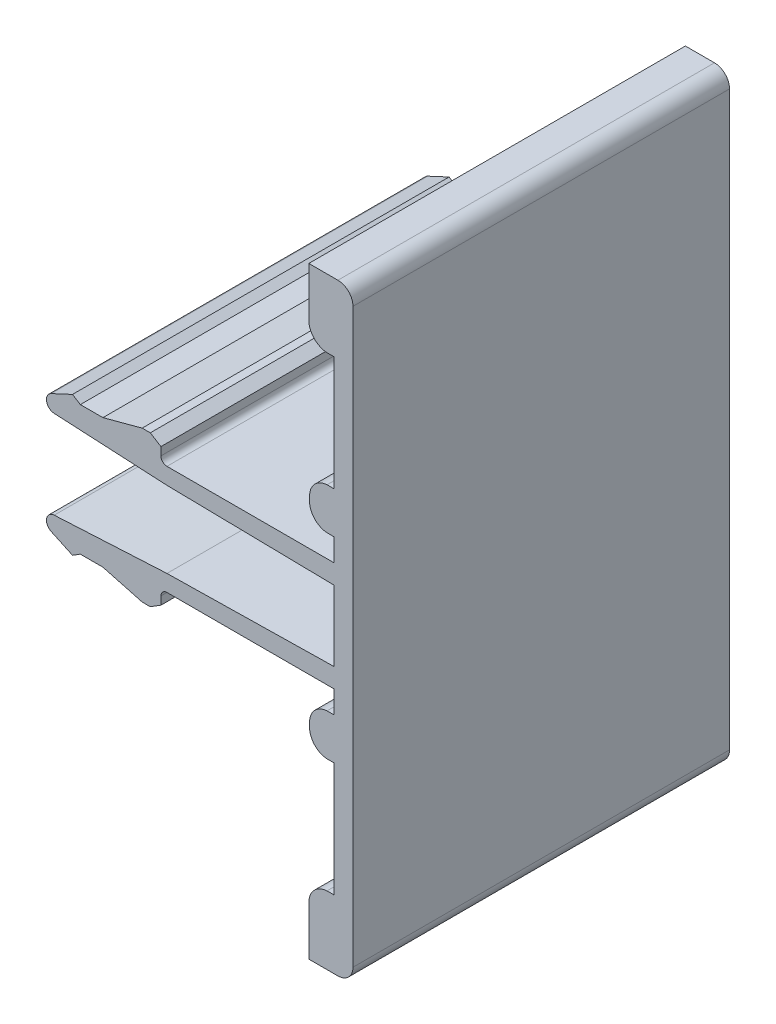
SolidWorks part; units mm, degrees
material "6005-T5"
ref_plane "Front" through (0, 0, 0) normal (0, 0, 1) x (1, 0, 0)
ref_plane "Top" through (0, 0, 0) normal (0, 1, 0) x (1, 0, 0)
ref_plane "Right" through (0, 0, 0) normal (1, 0, 0) x (0, 0, -1)
sketch "Sk Main Extrusion" plane through (0, 0, 0) normal (0, 0, 1) x (1, 0, 0)
  line L0 (-3.83, 2.5328) -> (-11.3125, 2.9251)
  line L5 (-3.83, -2.5328) -> (-11.3125, -2.9251)
  line L6 (6.7989, 7.8799) -> (7.27, 7.8799)
  line L7 (6.7989, 5.1201) -> (7.27, 5.1201)
  line L8 (6.7989, -5.1201) -> (7.27, -5.1201)
  line L9 (6.7989, -7.8799) -> (7.27, -7.8799)
  line L10 (6.7981, -15.47) -> (7.27, -15.47)
  line L11 (6.7981, 15.47) -> (7.27, 15.47)
  line L12 (5.638, 6.65) -> (5.638, 6.35)
  line L13 (7.27, 5.1201) -> (7.27, 3.625)
  line L14 (7.27, 3.625) -> (-3.83, 3.625)
  line L15 (-4.23, 4.025) -> (-4.23, 4.56)
  line L16 (-4.23, 4.56) -> (-4.9341, 5)
  line L17 (-4.9341, 5) -> (-5.4741, 5)
  line L18 (-5.4741, 5) -> (-8.08, 4.3)
  line L19 (-8.08, 4.3) -> (-9.58, 4.3)
  line L20 (-9.58, 4.3) -> (-10.1001, 4.625)
  line L21 (-10.1001, 4.625) -> (-11.5147, 3.9654)
  line L22 (-3.83, 2.5328) -> (7.27, 2.339)
  line L23 (7.27, 2.339) -> (7.27, -2.339)
  line L24 (7.27, -2.339) -> (-3.83, -2.5328)
  line L25 (-11.5147, -3.9654) -> (-10.1001, -4.625)
  line L26 (-10.1001, -4.625) -> (-9.58, -4.3)
  line L27 (-9.58, -4.3) -> (-8.08, -4.3)
  line L28 (-8.08, -4.3) -> (-5.4741, -5)
  line L29 (-5.4741, -5) -> (-4.9341, -5)
  line L30 (-4.9341, -5) -> (-4.23, -4.56)
  line L31 (-4.23, -4.56) -> (-4.23, -4.025)
  line L32 (-3.83, -3.625) -> (7.27, -3.625)
  line L33 (7.27, -3.625) -> (7.27, -5.1201)
  line L34 (5.638, -6.35) -> (5.638, -6.65)
  line L35 (7.27, -7.8799) -> (7.27, -15.47)
  line L36 (5.588, -16.75) -> (5.588, -20)
  line L37 (5.588, -20) -> (7.52, -20)
  line L38 (8.52, -19) -> (8.52, 19)
  line L39 (7.52, 20) -> (5.588, 20)
  line L40 (5.588, 20) -> (5.588, 16.75)
  line L41 (7.27, 15.47) -> (7.27, 7.8799)
  arc A0 (6.7989, 7.8799) -> (5.638, 6.65) centre (6.87, 6.65) ccw
  arc A1 (5.638, 6.35) -> (6.7989, 5.1201) centre (6.87, 6.35) ccw
  arc A2 (-4.23, 4.025) -> (-3.83, 3.625) centre (-3.83, 4.025) ccw
  arc A3 (-11.5147, 3.9654) -> (-11.3125, 2.9251) centre (-11.2839, 3.4704) ccw
  arc A4 (-11.3125, -2.9251) -> (-11.5147, -3.9654) centre (-11.2839, -3.4704) ccw
  arc A5 (-3.83, -3.625) -> (-4.23, -4.025) centre (-3.83, -4.025) ccw
  arc A6 (6.7989, -5.1201) -> (5.638, -6.35) centre (6.87, -6.35) ccw
  arc A7 (5.638, -6.65) -> (6.7989, -7.8799) centre (6.87, -6.65) ccw
  arc A8 (6.7981, -15.47) -> (5.588, -16.75) centre (6.87, -16.75) ccw
  arc A9 (7.52, -20) -> (8.52, -19) centre (7.52, -19) ccw
  arc A10 (8.52, 19) -> (7.52, 20) centre (7.52, 19) ccw
  arc A11 (5.588, 16.75) -> (6.7981, 15.47) centre (6.87, 16.75) ccw
  point P0 (0, 0)
extrude "Main Extrusion" add sketch "Sk Main Extrusion" against normal blind 25
equation "\"Weight kg\"= round ( \"SW-Mass\" , 2 )"
equation "\"Weight lbs\"= round ( \"SW-Mass\" * 2.2046 , 2 )"
equation "\"Length mm\"= round ( \"Length@Main Extrusion\" , 2 )"
equation "\"Length in\"= round ( \"Length@Main Extrusion\" / 25.4 , 3 )"
